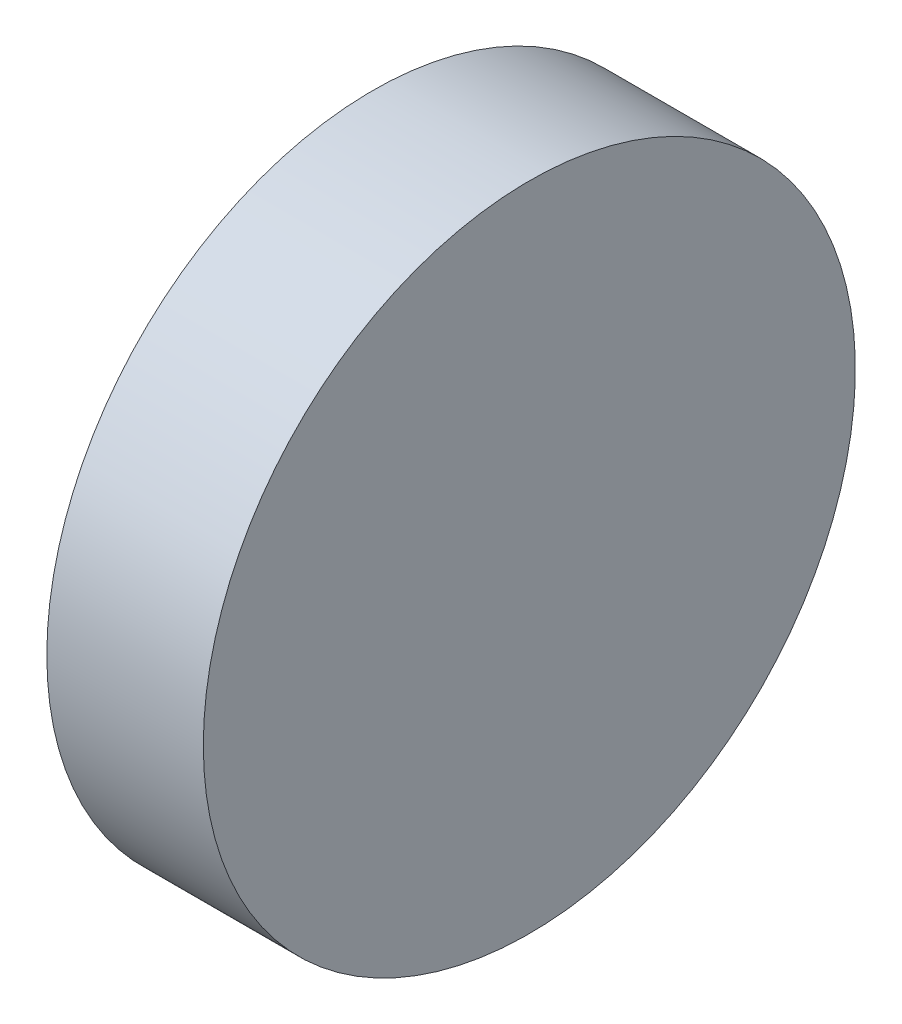
SolidWorks part; units mm, degrees
ref_plane "前视基准面" through (0, 0, 0) normal (0, 0, 1) x (1, 0, 0)
ref_plane "上视基准面" through (0, 0, 0) normal (0, 1, 0) x (1, 0, 0)
ref_plane "右视基准面" through (0, 0, 0) normal (1, 0, 0) x (0, 0, -1)
sketch "草图1" plane through (0, 0, 0) normal (0, 0, 1) x (1, 0, 0)
  line L0 (254.0008, 77.2932) -> (271.4723, 77.2932) construction
  line L1 (260.1571, 77.2932) -> (260.1571, 89.7932)
  line L2 (266.1571, 77.2932) -> (266.1571, 89.7932)
  line L3 (260.1571, 77.2932) -> (266.1571, 77.2932)
  line L5 (260.1571, 89.7932) -> (266.1571, 89.7932)
  dimension "D1" = 6
  dimension "D2" = 12.5
revolve "旋转1" add sketch "草图1" angle 360 about L0
